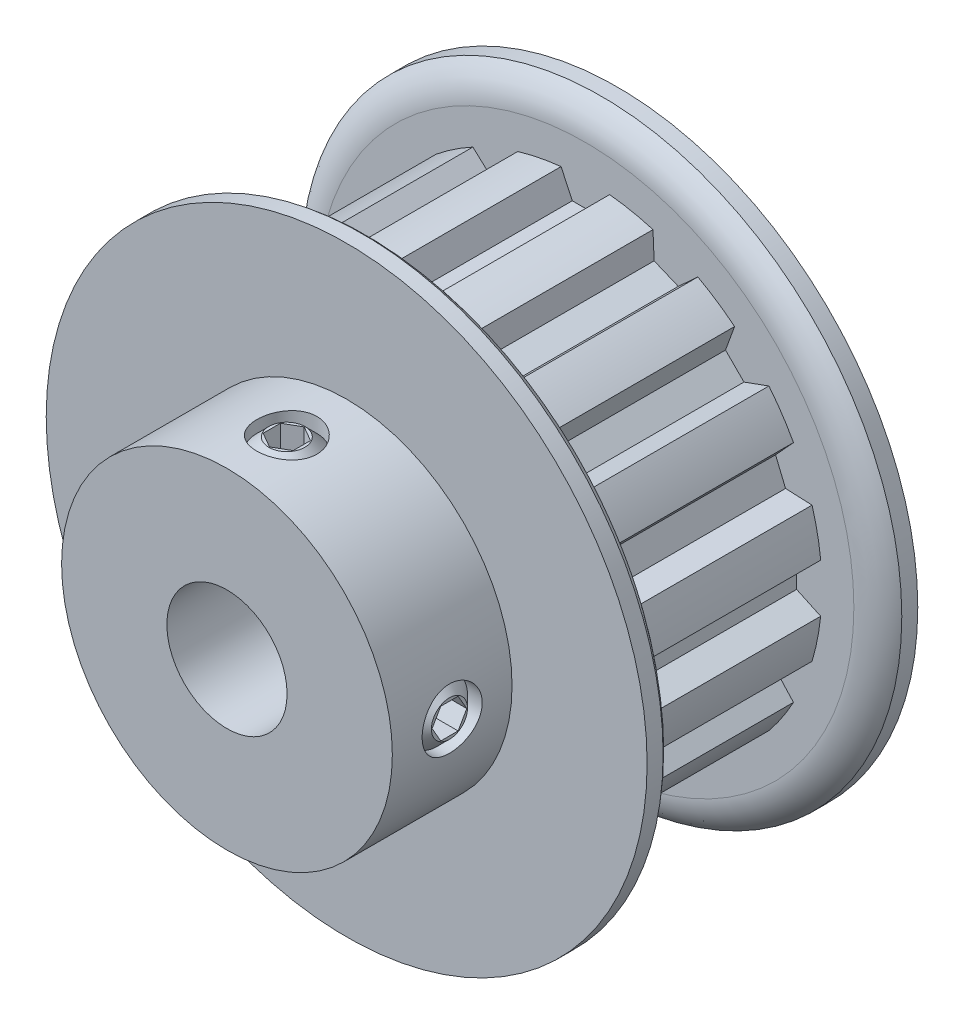
SolidWorks part; units mm, degrees
ref_plane "Front Plane" through (0, 0, 0) normal (0, 0, 1) x (1, 0, 0)
ref_plane "Top Plane" through (0, 0, 0) normal (0, 1, 0) x (1, 0, 0)
ref_plane "Right Plane" through (0, 0, 0) normal (1, 0, 0) x (0, 0, -1)
sketch "Sketch1" plane through (0, 0, 0) normal (0, 0, 1) x (1, 0, 0)
  line L0 (-1.2827, 12.4333) -> (-0.6905, 11.1633)
  line L1 (-0.6905, 11.1633) -> (0.6905, 11.1633)
  line L2 (0.6905, 11.1633) -> (1.2827, 12.4333)
  line L3 (-1.2827, 12.4333) -> (1.2827, 12.4333)
  line L4 (0, 0) -> (0, 11.1633) construction
  line L5 (0, 11.1633) -> (0, 13.4493) construction
  circle A0 centre (0, 0) radius 12.9413 construction
  circle A1 centre (0, 0) radius 15.875 construction
  circle A2 centre (0, 0) radius 12.4993 construction
  point P6 (0, 12.4333)
  point P11 (0, 12.9413)
  point P13 (0, 15.875)
  point P14 (0, 12.4993)
  dimension "D1" = 1.016
  dimension "D2" = 0.508
sketch "Sketch2" plane through (0, 0, 0) normal (1, 0, 0) x (0, 0, -1)
  line L0 (-10.3124, 3.175) -> (10.3124, 3.175)
  line L1 (-10.3124, 3.175) -> (-10.3124, 8.7376)
  line L2 (-10.3124, 8.7376) -> (-3.9878, 8.7376)
  line L3 (-3.9878, 8.7376) -> (-3.9878, 15.875)
  line L4 (-3.9878, 15.875) -> (-2.2987, 15.875) construction
  line L5 (-2.2987, 15.875) -> (-2.2987, 12.4993) construction
  line L6 (-2.2987, 12.4993) -> (8.6233, 12.4993)
  line L7 (8.6233, 12.4993) -> (8.6233, 15.875) construction
  line L8 (8.6233, 15.875) -> (10.3124, 15.875) construction
  line L9 (10.3124, 15.875) -> (10.3124, 3.175)
  line L10 (-10.3124, 0) -> (10.3124, 0) construction
  line L13 (-3.9878, 15.875) -> (-3.1432, 15.875)
  line L14 (-2.2987, 14.1871) -> (-2.2987, 12.4993)
  line L15 (8.6233, 12.4993) -> (8.6233, 14.1871)
  line L16 (9.4679, 15.875) -> (10.3124, 15.875)
  arc A0 (-2.2987, 14.1871) -> (-3.1432, 15.875) centre (-4.4076, 14.1871) ccw
  arc A1 (8.6233, 14.1871) -> (9.4679, 15.875) centre (10.7322, 14.1871) cw
  point P12 (-2.2987, 14.1871)
  point P14 (-3.1432, 15.875)
  point P20 (8.6233, 14.1871)
  point P21 (9.4679, 15.875)
  point P25 (8.6233, 0)
  point P26 (-2.2987, 0)
  dimension "Bore" = 6.35
  dimension "Hub Dia" = 17.4752
  dimension "Outside Width" = 14.3002
  dimension "Inside Width" = 10.922
revolve "Revolve1" add sketch "Sketch2" angle 360 mid plane about L10
sketch "Sketch3" plane through (0, 0, 0) normal (0, 0, 1) x (1, 0, 0)
  line L0 (-0.6905, 11.1633) -> (0.6905, 11.1633) construction
  line L1 (0.6905, 11.1633) -> (1.2827, 12.4333) construction
  line L2 (-1.2827, 12.4333) -> (-0.6905, 11.1633) construction
  line L3 (-0.6905, 11.1633) -> (0.6905, 11.1633)
  line L4 (0.6905, 11.1633) -> (1.2827, 12.4333)
  line L5 (-1.2827, 12.4333) -> (-0.6905, 11.1633)
  circle A0 centre (0, 0) radius 12.4993 construction
  arc A1 (1.2827, 12.4333) -> (-1.2827, 12.4333) centre (0, 0) ccw
extrude "Cut-Extrude1" cut sketch "Sketch3" against normal up to vertex (8.6233 mm away) from vertex at 2.2987 starting at point (0, 12.4993, 2.2987)
pattern_circular "CirPattern1" count 16 over 360 about axis through (0, 0, 0) along (0, 0, 1) of "Cut-Extrude1"
sketch "Sketch4" plane through (0, 0, 0) normal (0, 1, 0) x (1, 0, 0)
  line L0 (0, -3.9878) -> (0, -10.3124) construction
  line L1 (-8.7376, -3.9878) -> (8.7376, -3.9878) construction
  line L2 (-8.7376, -10.3124) -> (8.7376, -10.3124) construction
  circle A0 centre (0, -7.1501) radius 1.5875
  dimension "D1" = 3.175
extrude "Cut-Extrude2" cut sketch "Sketch4" along normal through all
ref_plane "Plane1" through (0, 0, 7.1501) normal (0, 0, 1) x (1, 0, 0)
sketch "Sketch5" plane through (0, 0, 7.1501) normal (0, 0, 1) x (1, 0, 0)
  line L0 (0, 0) -> (0, 8.7376) construction
  line L1 (-1.5875, 8.5922) -> (-1.5875, 2.7496) construction
  line L2 (-1.5875, 8.5922) -> (-1.5875, 2.7496) construction
  line L3 (0, 8.5922) -> (0, 3.175)
  line L4 (0, 3.175) -> (-0.9525, 3.175)
  line L5 (-1.5875, 7.9572) -> (-1.5875, 3.81)
  line L6 (-0.9525, 8.5922) -> (0, 8.5922)
  line L7 (-1.5875, 7.9572) -> (-0.9525, 8.5922)
  line L8 (-1.5875, 3.81) -> (-0.9525, 3.175)
  circle A0 centre (0, 0) radius 8.7376 construction
  circle A3 centre (0, 0) radius 3.175 construction
  point P13 (-1.5875, 3.175)
  point P15 (-1.5875, 8.5922)
revolve "Revolve2" add sketch "Sketch5" angle 360 mid plane about L0
sketch "Sketch6" plane through (0, 8.5922, 0) normal (0, -1, 0) x (-1, 0, 0)
  line L1 (0, -6.2336) -> (-0.7938, -6.6918)
  line L2 (-0.7938, -6.6918) -> (-0.7937, -7.6084)
  line L3 (-0.7937, -7.6084) -> (0, -8.0666)
  line L4 (0, -8.0666) -> (0.7938, -7.6084)
  line L5 (0.7938, -7.6084) -> (0.7938, -6.6918)
  line L6 (0.7938, -6.6918) -> (0, -6.2336)
  circle A0 centre (0, -7.1501) radius 0.7938 construction
  dimension "D1" = 1.5875
extrude "Cut-Extrude3" cut sketch "Sketch6" along normal blind 1.1906
pattern_circular "CirPattern2" count 2 every 90 about axis through (0, 0, 0) along (0, 0, 1) of "Cut-Extrude2", "Revolve2", "Cut-Extrude3"
equation "\"D2@Sketch1\" = \"D1@Sketch1\"/2"
equation "\"D1@Sketch4\" = \"Bore@Sketch2\"/2"
equation "\"D1@Sketch6\" = \"D1@Sketch4\"/2"
equation "\"D1@Cut-Extrude3\" = \"D1@Sketch6\"*.75"
